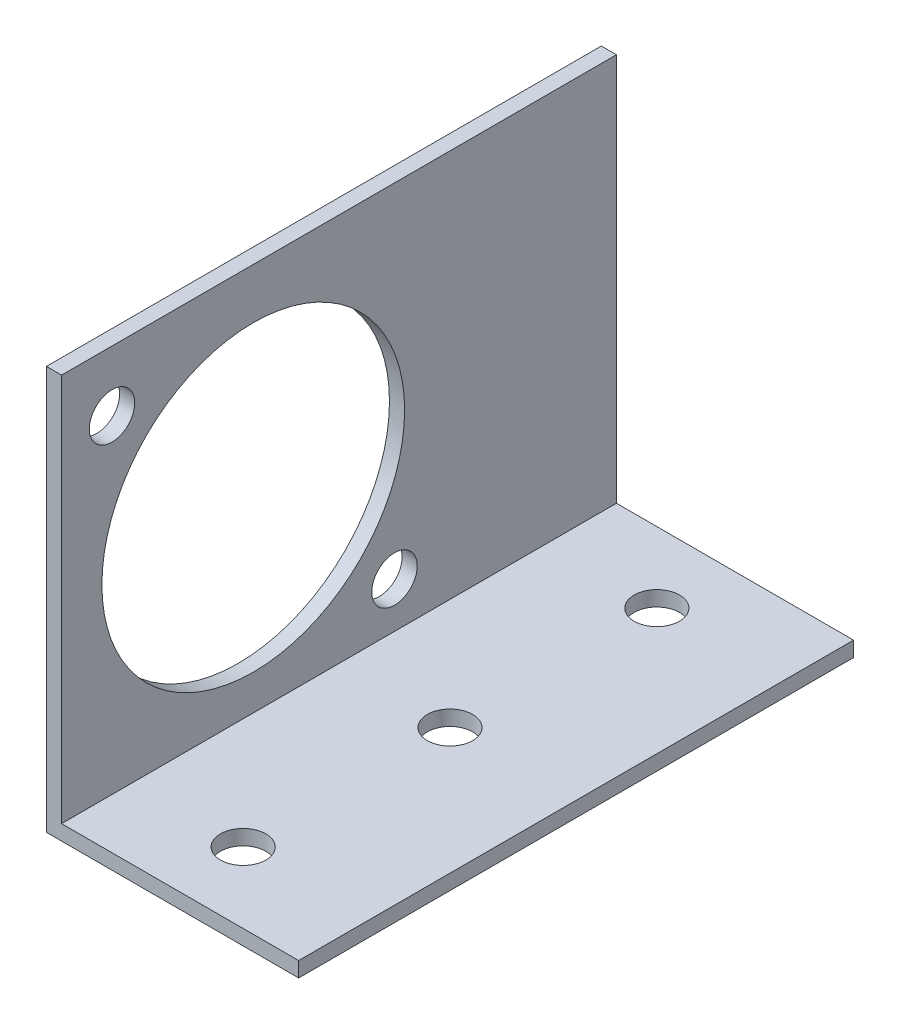
SolidWorks part; units mm, degrees
ref_plane "Plan de face" through (0, 0, 0) normal (0, 0, 1) x (1, 0, 0)
ref_plane "Plan de dessus" through (0, 0, 0) normal (0, 1, 0) x (1, 0, 0)
ref_plane "Plan de droite" through (0, 0, 0) normal (1, 0, 0) x (0, 0, -1)
sketch "Esquisse1" plane through (0, 0, 0) normal (0, 0, 1) x (1, 0, 0)
  line L0 (0, 0) -> (25, 0)
  line L1 (0, 0) -> (0, 40)
  dimension "D1" = 40
  dimension "D2" = 25
extrude "Extru.-Mince1" add sketch "Esquisse1" against normal blind 55 thin thin type one direction wall 1.5
sketch "Esquisse2" plane through (0, 1.5, 0) normal (0, 1, 0) x (-1, 0, 0)
  line L0 (-25, 0) -> (-1.5, 0) construction
  line L1 (-25, -55) -> (-1.5, -55) construction
  line L2 (-25, -55) -> (-25, 0) construction
  point P0 (-12.5, -7)
  point P1 (-12.5, -27.5)
  point P2 (-12.5, -48)
  dimension "D1" = 7
  dimension "D2" = 7
  dimension "D3" = 27.5
  dimension "D4" = 12.5
  dimension "D5" = 12.5
  dimension "D6" = 12.5
hole_wizard "Dégagement M41" positions "Esquisse8" profile "Esquisse9" hole size "M4" standard "ISO" end condition through all
sketch "Esquisse8" plane through (0, 1.5, 0) normal (0, 1, 0) x (-1, 0, 0)
  point P1 (-12.5, -7)
  point P4 (-12.5, -27.5)
  point P7 (-12.5, -48)
sketch "Esquisse9" plane through (12.5, 1.5, -7) normal (1, 0, 0) x (0, 0, 1)
  line L0 (0, 0) -> (0, 1.5)
  line L1 (0, 1.5) -> (2.25, 1.5)
  line L2 (2.25, 1.5) -> (2.25, 0)
  line L5 (2.25, 0) -> (0, 0)
  line L11 (0, -6.35) -> (0, 107.95) construction
  dimension "Diamètre du perçage jusqu'au prochain" = 4.5
  dimension "Profondeur du perçage jusqu'au prochain" = 1.5
sketch "Esquisse10" plane through (1.5, 0, 0) normal (1, 0, 0) x (0, 0, -1)
  line L0 (55, 40) -> (0, 40) construction
  line L1 (0, 1.5) -> (0, 40) construction
  point P0 (19, 20)
  point P5 (33, 6)
  point P6 (5, 34)
  dimension "D1" = 20
  dimension "D2" = 19
  dimension "D3" = 5
  dimension "D4" = 6
  dimension "D5" = 34
  dimension "D6" = 33
hole_wizard "Dégagement M42" positions "Esquisse12" profile "Esquisse11" hole size "M4" standard "ISO" end condition through all
sketch "Esquisse12" plane through (1.5, 0, 0) normal (1, 0, 0) x (0, 0, -1)
  point P1 (5, 34)
  point P4 (33, 6)
sketch "Esquisse11" plane through (1.5, 34, -5) normal (0, 1, 0) x (0, 0, -1)
  line L0 (0, 0) -> (0, 1.5)
  line L1 (0, 1.5) -> (2.25, 1.5)
  line L2 (2.25, 1.5) -> (2.25, 0)
  line L5 (2.25, 0) -> (0, 0)
  line L11 (0, -6.35) -> (0, 107.95) construction
  dimension "Diamètre du perçage jusqu'au prochain" = 4.5
  dimension "Profondeur du perçage jusqu'au prochain" = 1.5
hole_wizard "Dégagement M271" positions "Esquisse14" profile "Esquisse13" hole size "M27" standard "ISO"
sketch "Esquisse14" plane through (1.5, 0, 0) normal (1, 0, 0) x (0, 0, -1)
  point P1 (19, 20)
sketch "Esquisse13" plane through (1.5, 20, -19) normal (0, 1, 0) x (0, 0, -1)
  line L0 (0, 0) -> (0, 10.5129)
  line L1 (0, 10.5129) -> (15, 1.5)
  line L2 (15, 1.5) -> (15, 0)
  line L5 (15, 0) -> (0, 0)
  line L10 (0, 10.5129) -> (-15, 1.5) construction
  line L11 (0, -6.35) -> (0, 107.95) construction
  dimension "Diamètre du perçage" = 30
  dimension "Profondeur du perçage" = 1.5
  dimension "Angle de pointe" = 118
